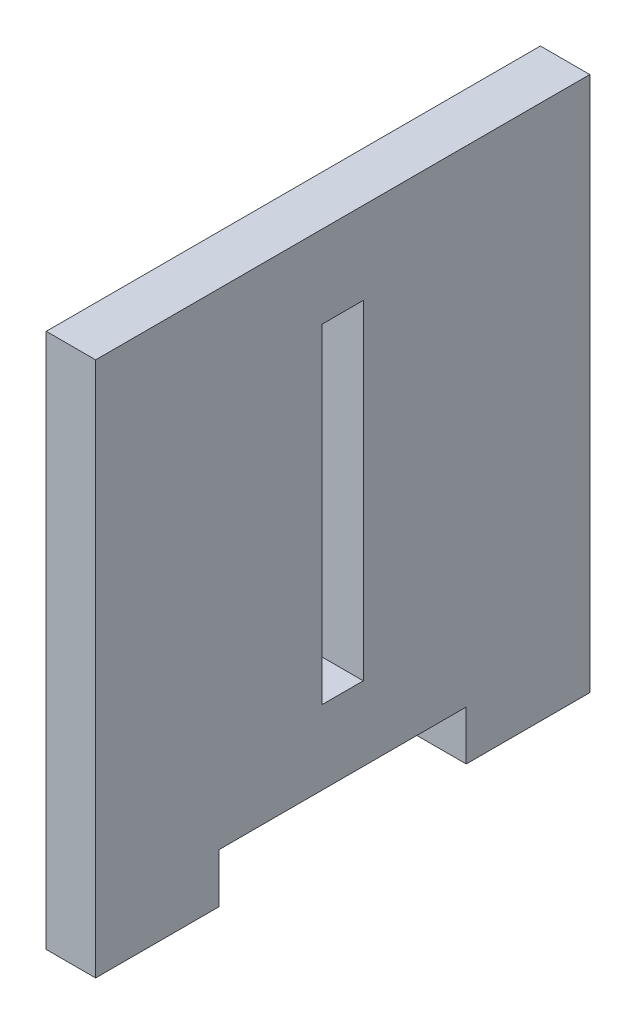
SolidWorks part; units mm, degrees
ref_plane "Front Plane" through (0, 0, 0) normal (0, 0, 1) x (1, 0, 0)
ref_plane "Top Plane" through (0, 0, 0) normal (0, 1, 0) x (1, 0, 0)
ref_plane "Right Plane" through (0, 0, 0) normal (1, 0, 0) x (0, 0, -1)
sketch "Sketch1" plane through (0, 0, 0) normal (1, 0, 0) x (0, 0, -1)
  line L0 (-15, 0) -> (0, 0)
  line L1 (-60, 65) -> (0, 65)
  line L2 (-60, 65) -> (-60, 0)
  line L3 (-60, 0) -> (-45, 0)
  line L4 (0, 65) -> (0, 0)
  line L6 (-45, 0) -> (-45, 6)
  line L7 (-45, 6) -> (-15, 6)
  line L8 (-15, 0) -> (-15, 6)
  line L10 (-32.5, 55) -> (-27.5, 55)
  line L11 (-32.5, 55) -> (-32.5, 15)
  line L12 (-32.5, 15) -> (-27.5, 15)
  line L13 (-27.5, 55) -> (-27.5, 15)
  point P13 (-30, 55)
  point P14 (-30, 65)
  dimension "D1" = 60
  dimension "D2" = 65
  dimension "D3" = 15
  dimension "D4" = 15
  dimension "D5" = 6
  dimension "D6" = 5
  dimension "D7" = 10
  dimension "D8" = 40
extrude "Boss-Extrude1" add sketch "Sketch1" along normal blind 6
